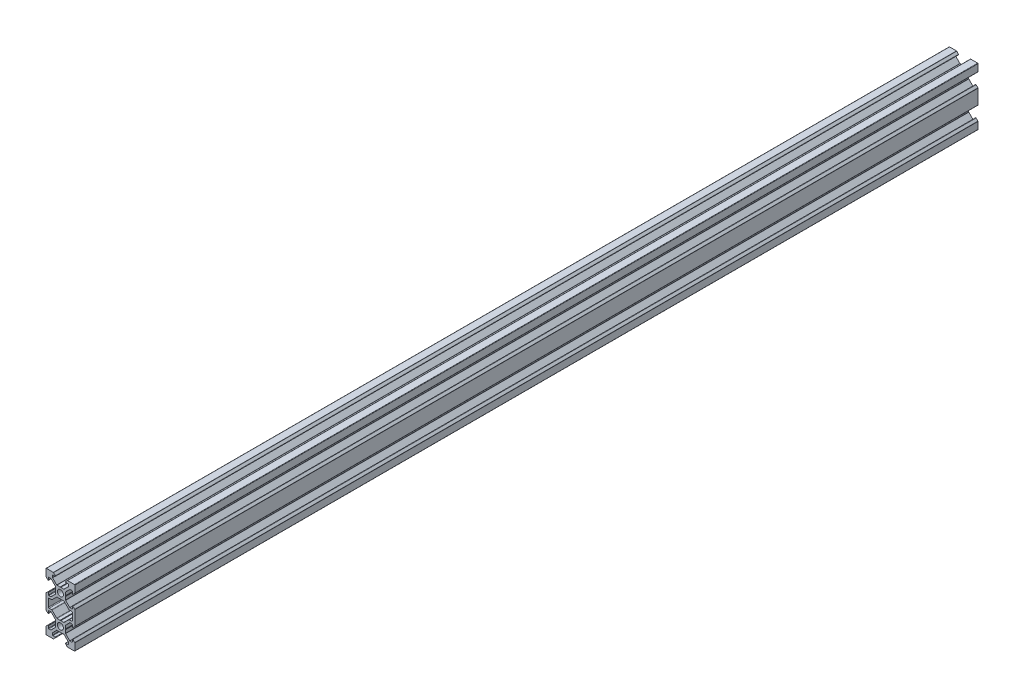
SolidWorks part; units mm, degrees
ref_plane "Front Plane" through (0, 0, 0) normal (0, 0, 1) x (1, 0, 0)
ref_plane "Top Plane" through (0, 0, 0) normal (0, 1, 0) x (1, 0, 0)
ref_plane "Right Plane" through (0, 0, 0) normal (1, 0, 0) x (0, 0, -1)
sketch "Sketch1" plane through (0, 0, 0) normal (0, 0, 1) x (1, 0, 0)
  line L0 (3.5607, 3.5607) -> (10.6317, 10.6317) construction
  line L1 (2.5, -3.5607) -> (-2.5, -3.5607)
  line L2 (3.5607, -2.5) -> (3.5607, 2.5)
  line L3 (2.5, 3.5607) -> (-2.5, 3.5607)
  line L4 (-3.5607, -2.5) -> (-3.5607, 2.5)
  line L5 (3.5607, -3.5607) -> (-3.5607, 3.5607) construction
  line L6 (3.5607, 3.5607) -> (-3.5607, -3.5607) construction
  line L7 (2.5, 3.5607) -> (5.5, 6.5607)
  line L8 (5.5, 6.5607) -> (5.5, 8.2521)
  line L9 (5.5, 8.2521) -> (3.1, 8.2521)
  line L10 (3.1, 8.2521) -> (4.8479, 10)
  line L11 (4.8479, 10) -> (10, 10)
  line L12 (3.5607, 2.5) -> (6.5607, 5.5)
  line L13 (6.5607, 5.5) -> (8.2521, 5.5)
  line L14 (8.2521, 5.5) -> (8.2521, 3.1)
  line L15 (8.2521, 3.1) -> (10, 4.8479)
  line L16 (10, 4.8479) -> (10, 10)
  line L17 (0, -55) -> (0, 55) construction
  line L18 (-3.5607, 3.5607) -> (-10.6317, 10.6317) construction
  line L19 (-10, 4.8479) -> (-10, 10)
  line L20 (-8.2521, 3.1) -> (-10, 4.8479)
  line L21 (-8.2521, 5.5) -> (-8.2521, 3.1)
  line L22 (-6.5607, 5.5) -> (-8.2521, 5.5)
  line L23 (-3.5607, 2.5) -> (-6.5607, 5.5)
  line L24 (-4.8479, 10) -> (-10, 10)
  line L25 (-3.1, 8.2521) -> (-4.8479, 10)
  line L26 (-5.5, 8.2521) -> (-3.1, 8.2521)
  line L27 (-5.5, 6.5607) -> (-5.5, 8.2521)
  line L28 (-2.5, 3.5607) -> (-5.5, 6.5607)
  line L29 (-8.2521, -7) -> (-5.9393, -7)
  line L30 (55, 0) -> (-55, 0) construction
  line L31 (-3.5607, -3.5607) -> (-10.6317, -10.6317) construction
  line L32 (3.5607, -3.5607) -> (10.6317, -10.6317) construction
  line L33 (-2.5, -3.5607) -> (-5.5, -6.5607)
  line L34 (-5.5, -6.5607) -> (-5.9393, -7)
  line L35 (5.5, -6.5607) -> (5.9393, -7)
  line L36 (8.2521, -7) -> (5.9393, -7)
  line L37 (-12.2633, -10) -> (14.5346, -10) construction
  line L38 (-3.5607, -2.5) -> (-6.5607, -5.5)
  line L39 (-6.5607, -5.5) -> (-8.2521, -5.5)
  line L40 (-8.2521, -5.5) -> (-8.2521, -3.1)
  line L41 (-8.2521, -3.1) -> (-10, -4.8479)
  line L42 (-10, -4.8479) -> (-10, -7)
  line L43 (10, -4.8479) -> (10, -7)
  line L44 (8.2521, -3.1) -> (10, -4.8479)
  line L45 (8.2521, -5.5) -> (8.2521, -3.1)
  line L46 (6.5607, -5.5) -> (8.2521, -5.5)
  line L47 (3.5607, -2.5) -> (6.5607, -5.5)
  line L48 (-3.5607, -23.5607) -> (-10.6317, -30.6317) construction
  line L49 (3.5607, -23.5607) -> (-3.5607, -16.4393) construction
  line L50 (3.5607, -16.4393) -> (-3.5607, -23.5607) construction
  line L51 (3.5607, -23.5607) -> (10.6317, -30.6317) construction
  line L52 (2.5, -3.5607) -> (5.5, -6.5607)
  line L53 (2.5, -16.4393) -> (5.5, -13.4393)
  line L54 (3.5607, -17.5) -> (6.5607, -14.5)
  line L55 (6.5607, -14.5) -> (8.2521, -14.5)
  line L56 (8.2521, -14.5) -> (8.2521, -16.9)
  line L57 (8.2521, -16.9) -> (10, -15.1521)
  line L58 (10, -15.1521) -> (10, -13)
  line L59 (-10, -15.1521) -> (-10, -13)
  line L60 (-8.2521, -16.9) -> (-10, -15.1521)
  line L61 (-8.2521, -14.5) -> (-8.2521, -16.9)
  line L62 (-6.5607, -14.5) -> (-8.2521, -14.5)
  line L63 (-3.5607, -17.5) -> (-6.5607, -14.5)
  line L64 (8.2521, -13) -> (5.9393, -13)
  line L65 (5.5, -13.4393) -> (5.9393, -13)
  line L66 (-5.5, -13.4393) -> (-5.9393, -13)
  line L67 (-2.5, -16.4393) -> (-5.5, -13.4393)
  line L68 (-8.2521, -13) -> (-5.9393, -13)
  line L69 (-2.5, -23.5607) -> (-5.5, -26.5607)
  line L70 (-5.5, -26.5607) -> (-5.5, -28.2521)
  line L71 (-5.5, -28.2521) -> (-3.1, -28.2521)
  line L72 (-3.1, -28.2521) -> (-4.8479, -30)
  line L73 (-4.8479, -30) -> (-10, -30)
  line L74 (-3.5607, -22.5) -> (-6.5607, -25.5)
  line L75 (-6.5607, -25.5) -> (-8.2521, -25.5)
  line L76 (-8.2521, -25.5) -> (-8.2521, -23.1)
  line L77 (-8.2521, -23.1) -> (-10, -24.8479)
  line L78 (-10, -24.8479) -> (-10, -30)
  line L79 (10, -24.8479) -> (10, -30)
  line L80 (8.2521, -23.1) -> (10, -24.8479)
  line L81 (8.2521, -25.5) -> (8.2521, -23.1)
  line L82 (6.5607, -25.5) -> (8.2521, -25.5)
  line L83 (3.5607, -22.5) -> (6.5607, -25.5)
  line L84 (4.8479, -30) -> (10, -30)
  line L85 (3.1, -28.2521) -> (4.8479, -30)
  line L86 (5.5, -28.2521) -> (3.1, -28.2521)
  line L87 (5.5, -26.5607) -> (5.5, -28.2521)
  line L88 (2.5, -23.5607) -> (5.5, -26.5607)
  line L89 (-3.5607, -17.5) -> (-3.5607, -22.5)
  line L90 (2.5, -23.5607) -> (-2.5, -23.5607)
  line L91 (3.5607, -17.5) -> (3.5607, -22.5)
  line L92 (2.5, -16.4393) -> (-2.5, -16.4393)
  line L93 (-10, -7) -> (-10, -13)
  line L94 (-8.2521, -13) -> (-8.2521, -7)
  line L95 (8.2521, -13) -> (8.2521, -7)
  line L96 (10, -7) -> (10, -13)
  circle A0 centre (0, 0) radius 2.1
  circle A1 centre (0, -20) radius 2.1
  point P0 (0, 0)
  point P102 (0, -20)
  dimension "D10" = 4.2
  dimension "D11" = 4.2
  dimension "D1" = 1.5
  dimension "D2" = 10
  dimension "D3" = 20
  dimension "D4" = 6.2
  dimension "D5" = 11
  dimension "D6" = 45
  dimension "D7" = 1.5
  dimension "D8" = 10
  dimension "D9" = 5
extrude "Boss-Extrude1" add sketch "Sketch1" along normal blind 627
fillet "Fillet1" radius 0.25 64 edges at (5.5, 6.5607, 313.5) (5.5, 8.2521, 313.5) (3.1, 8.2521, 313.5) (4.8479, 10, 313.5) (10, 10, 313.5) (10, 4.8479, 313.5) (8.2521, 3.1, 313.5) (8.2521, 5.5, 313.5) (6.5607, 5.5, 313.5) (3.5607, 2.5, 313.5) (3.5607, -2.5, 313.5) (6.5607, -5.5, 313.5) (8.2521, -5.5, 313.5) (8.2521, -3.1, 313.5) (10, -4.8479, 313.5) (10, -15.1521, 313.5) (8.2521, -16.9, 313.5) (8.2521, -14.5, 313.5) (6.5607, -14.5, 313.5) (3.5607, -17.5, 313.5) (3.5607, -22.5, 313.5) (6.5607, -25.5, 313.5) (8.2521, -25.5, 313.5) (8.2521, -23.1, 313.5) (10, -24.8479, 313.5) (10, -30, 313.5) (4.8479, -30, 313.5) (3.1, -28.2521, 313.5) (5.5, -28.2521, 313.5) (5.5, -26.5607, 313.5) (2.5, -23.5607, 313.5) (-2.5, -23.5607, 313.5) (-5.5, -26.5607, 313.5) (-5.5, -28.2521, 313.5) (-3.1, -28.2521, 313.5) (-4.8479, -30, 313.5) (-10, -30, 313.5) (-10, -24.8479, 313.5) (-8.2521, -23.1, 313.5) (-8.2521, -25.5, 313.5) (-6.5607, -25.5, 313.5) (-3.5607, -22.5, 313.5) (-3.5607, -17.5, 313.5) (-6.5607, -14.5, 313.5) (-8.2521, -14.5, 313.5) (-8.2521, -16.9, 313.5) (-10, -15.1521, 313.5) (-10, -4.8479, 313.5) (-8.2521, -3.1, 313.5) (-8.2521, -5.5, 313.5) (-6.5607, -5.5, 313.5) (-3.5607, -2.5, 313.5) (-3.5607, 2.5, 313.5) (-6.5607, 5.5, 313.5) (-8.2521, 5.5, 313.5) (-8.2521, 3.1, 313.5) (-10, 4.8479, 313.5) (-10, 10, 313.5) (-4.8479, 10, 313.5) (-5.5, 8.2521, 313.5) (-5.5, 6.5607, 313.5) (-2.5, 3.5607, 313.5) (2.5, 3.5607, 313.5) (-3.1, 8.2521, 313.5)
fillet "Fillet2" radius 0.5 12 edges at (-5.9393, -7, 313.5) (-8.2521, -7, 313.5) (-8.2521, -13, 313.5) (-5.9393, -13, 313.5) (-2.5, -16.4393, 313.5) (2.5, -16.4393, 313.5) (8.2521, -7, 313.5) (5.9393, -7, 313.5) (2.5, -3.5607, 313.5) (-2.5, -3.5607, 313.5) (5.9393, -13, 313.5) (8.2521, -13, 313.5)
sketch "Sketch2" plane through (0, 0, 627) normal (0, 0, 1) x (1, 0, 0)
  line L4 (0, 3.5607) -> (0, 3.1447) construction
  line L5 (2.3964, 3.5607) -> (-2.3964, 3.5607) construction
  line L6 (0, 3.399) -> (-0.2423, 3.5607)
  line L7 (0, 3.399) -> (0.2423, 3.5607)
  line L8 (-0.2423, 3.5607) -> (0.2423, 3.5607)
  line L9 (55, 0) -> (-55, 0) construction
  line L10 (0, -3.5607) -> (0, -3.1447) construction
  line L11 (0, -3.399) -> (0.2423, -3.5607)
  line L12 (0, -3.399) -> (-0.2423, -3.5607)
  line L13 (-0.2423, -3.5607) -> (0.2423, -3.5607)
  line L14 (0, 0) -> (-4.0856, 4.0856) construction
  line L15 (-8.2521, -10) -> (4.1581, -10) construction
  line L16 (-8.2521, -7.5) -> (-8.2521, -12.5) construction
  line L17 (3.5607, 0) -> (3.1447, 0) construction
  line L18 (3.5607, 0.2423) -> (3.5607, -0.2423)
  line L19 (3.399, 0) -> (3.5607, 0.2423)
  line L20 (3.399, 0) -> (3.5607, -0.2423)
  line L21 (-3.5607, 0) -> (-3.1447, 0) construction
  line L22 (-3.5607, 0.2423) -> (-3.5607, -0.2423)
  line L23 (-3.399, 0) -> (-3.5607, -0.2423)
  line L24 (-3.399, 0) -> (-3.5607, 0.2423)
  line L25 (-3.5607, -20) -> (-3.1447, -20) construction
  line L26 (3.5607, -20) -> (3.1447, -20) construction
  line L27 (0, -20) -> (-4.0856, -24.0856) construction
  line L28 (0, -16.4393) -> (0, -16.8553) construction
  line L29 (0, -23.5607) -> (0, -23.1447) construction
  line L30 (-3.399, -20) -> (-3.5607, -20.2423)
  line L31 (-3.399, -20) -> (-3.5607, -19.7577)
  line L32 (-3.5607, -20.2423) -> (-3.5607, -19.7577)
  line L33 (3.399, -20) -> (3.5607, -19.7577)
  line L34 (3.399, -20) -> (3.5607, -20.2423)
  line L35 (3.5607, -20.2423) -> (3.5607, -19.7577)
  line L36 (-0.2423, -16.4393) -> (0.2423, -16.4393)
  line L37 (0, -16.601) -> (-0.2423, -16.4393)
  line L38 (0, -16.601) -> (0.2423, -16.4393)
  line L39 (-0.2423, -23.5607) -> (0.2423, -23.5607)
  line L40 (0, -23.399) -> (0.2423, -23.5607)
  line L41 (0, -23.399) -> (-0.2423, -23.5607)
extrude "Cut-Extrude1" cut sketch "Sketch2" against normal through all
